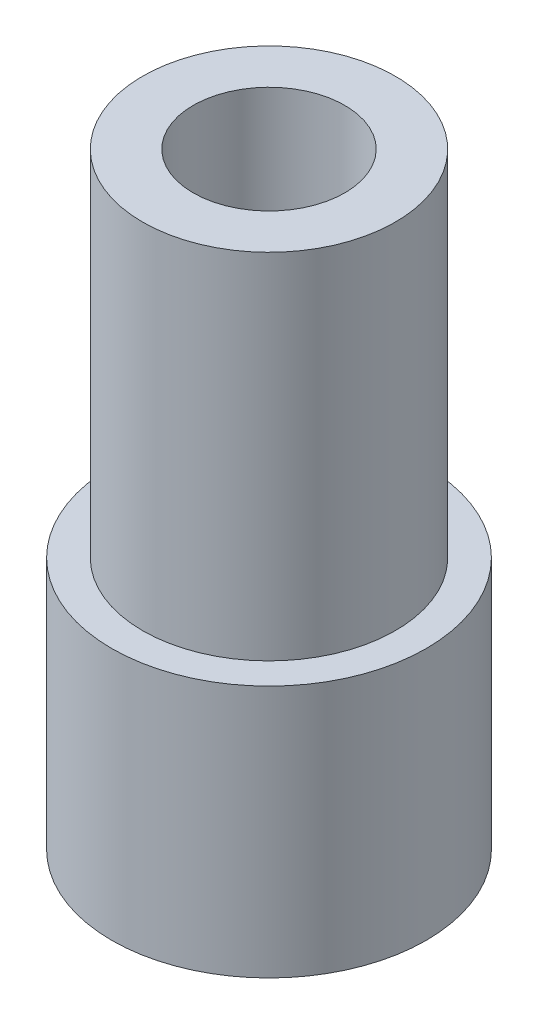
SolidWorks part; units mm, degrees
ref_plane "Plan de face" through (0, 0, 0) normal (0, 0, 1) x (1, 0, 0)
ref_plane "Plan de dessus" through (0, 0, 0) normal (0, 1, 0) x (1, 0, 0)
ref_plane "Plan de droite" through (0, 0, 0) normal (1, 0, 0) x (0, 0, -1)
sketch "Esquisse1" plane through (0, 0, 0) normal (0, 0, 1) x (1, 0, 0)
  line L0 (0, 8.6266) -> (0, -8.6266) construction
  line L1 (1.5, 3.5) -> (1.5, -8.5)
  line L2 (1.5, -8.5) -> (3.1111, -8.5)
  line L3 (3.1111, -8.5) -> (3.1111, -3.5)
  line L6 (3.1111, -3.5) -> (2.5, -3.5)
  line L7 (2.5, -3.5) -> (2.5, 3.5)
  line L12 (2.5, 3.5) -> (1.5, 3.5)
  line L13 (0, 0) -> (37.2784, 0) construction
  dimension "D1" = 7
  dimension "D2" = 5
  dimension "D3" = 3
  dimension "D4" = 6.2222
  dimension "D5" = 12
revolve "Révolution1" add sketch "Esquisse1" angle 360 about L0
